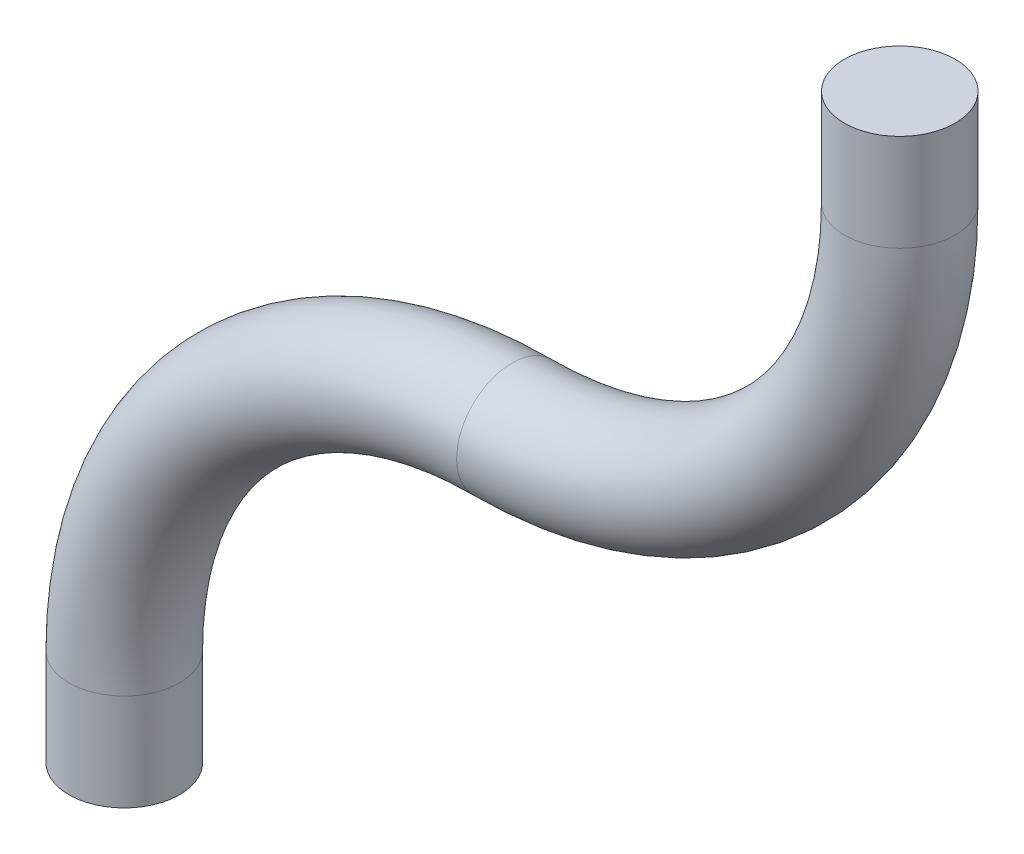
SolidWorks part; units mm, degrees
ref_plane "Plan de face" through (0, 0, 0) normal (0, 0, 1) x (1, 0, 0)
ref_plane "Plan de dessus" through (0, 0, 0) normal (0, 1, 0) x (1, 0, 0)
ref_plane "Plan de droite" through (0, 0, 0) normal (1, 0, 0) x (0, 0, -1)
sketch "Esquisse1" plane through (0, 0, 0) normal (0, 0, 1) x (1, 0, 0)
  line L0 (0, 0) -> (0, -5.6)
  line L1 (44.8, 44.8) -> (44.8, 50.4)
  arc A0 (0, 0) -> (22.4, 22.4) centre (22.4, 0) cw
  arc A1 (22.4, 22.4) -> (44.8, 44.8) centre (22.4, 44.8) ccw
sweep "Balayage1" add path "Esquisse1" circular profile diameter 6.4 parameters "D3"=6.4
